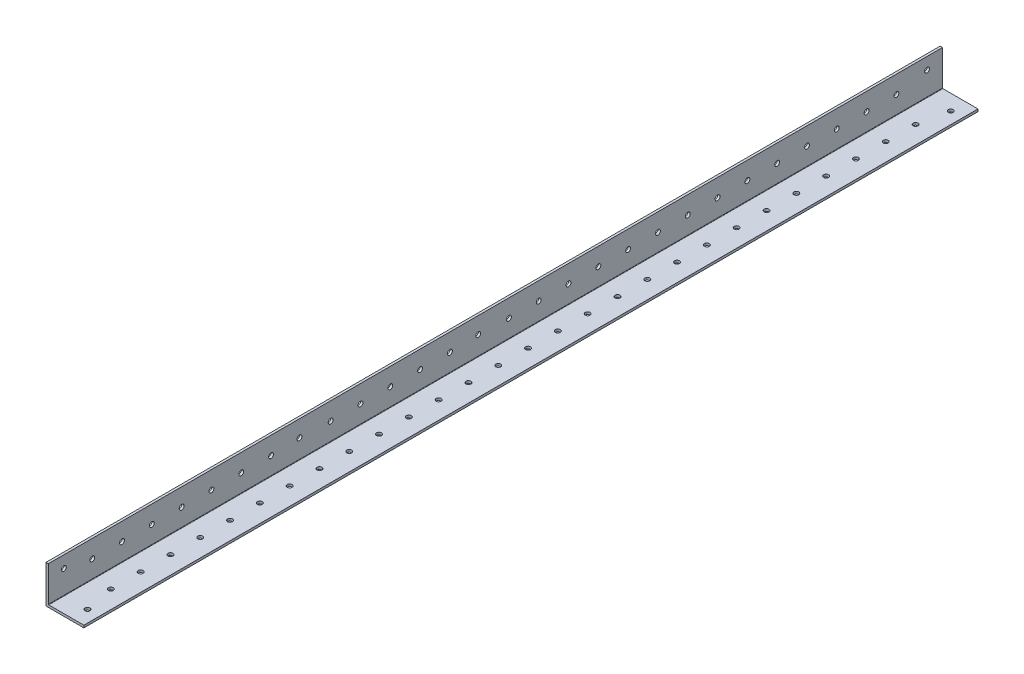
SolidWorks part; units mm, degrees
material "6061 Alloy"
ref_plane "Front Plane" through (0, 0, 0) normal (0, 0, 1) x (1, 0, 0)
ref_plane "Top Plane" through (0, 0, 0) normal (0, 1, 0) x (1, 0, 0)
ref_plane "Right Plane" through (0, 0, 0) normal (1, 0, 0) x (0, 0, -1)
sketch "Sketch1" plane through (0, 0, 0) normal (0, 0, 1) x (1, 0, 0)
  line L0 (0, 25.4) -> (0, 0) construction
  line L1 (0, 0) -> (25.4, 0) construction
  line L2 (25.4, 0) -> (25.4, 1.5875) construction
  line L3 (25.4, 1.5875) -> (1.5875, 1.5875) construction
  line L4 (1.5875, 1.5875) -> (1.5875, 25.4) construction
  line L6 (1.5875, 25.4) -> (0, 25.4) construction
  arc A0 (1.5875, 1.8415) -> (1.8415, 1.5875) centre (1.8415, 1.8415) ccw construction
  point P4 (0, 0)
  dimension "Inside Corner Radius" = 0.254
  dimension "Outside Height" = 25.4
  dimension "Inside Height" = 23.8125
  dimension "Outside Width" = 25.4
  dimension "Inside Width" = 23.8125
  dimension "Wall Thickness" = 1.5875
  dimension "Shape" = 90
sketch "Sketch2" plane through (0, 0, 0) normal (1, 0, 0) x (0, 0, -1)
  line L0 (1219.2, 0) -> (-1219.2, 0) construction
  line L1 (-1219.2, 25.4) -> (-1219.2, 0) construction
  line L2 (1219.2, 25.4) -> (1219.2, 0) construction
  point P0 (-1189.99, 0)
  point P4 (0, 0)
  point P6 (1189.99, 0)
  dimension "D1" = 29.21
  dimension "D2" = 29.21
  dimension "D3" = 25.4
  dimension "Length" = 2438.4
sketch "Sketch3" plane through (0, 0, 0) normal (0, 0, 1) x (1, 0, 0)
  line L0 (1.5875, 25.4) -> (0, 25.4)
  line L1 (0, 25.4) -> (0, 0)
  line L2 (0, 0) -> (25.4, 0)
  line L3 (25.4, 0) -> (25.4, 1.5875)
  line L4 (25.4, 1.5875) -> (1.5875, 1.5875)
  line L5 (1.5875, 1.5875) -> (1.5875, 25.4)
extrude "Boss-Extrude1" add sketch "Sketch3" along normal mid plane 2438.4
fillet "Fillet1" radius 0.254 1 edges at (1.5875, 1.5875, 0)
sketch "Sketch4" plane through (0, 0, 0) normal (-1, 0, 0) x (0, 0, 1)
  line L0 (1219.2, 25.4) -> (1219.2, 0) construction
  line L1 (-1219.2, 0) -> (619.2, 0)
  line L2 (-1219.2, 0) -> (-1219.2, 74.9453)
  line L3 (-1219.2, 74.9453) -> (619.2, 74.9453)
  line L4 (619.2, 0) -> (619.2, 74.9453)
  dimension "D1" = 600
extrude "Cut-Extrude1" cut sketch "Sketch4" against normal blind 60
sketch "Sketch5" plane through (0, 1.5875, 0) normal (0, 1, 0) x (1, 0, 0)
  line L0 (17.4625, -1208.8241) -> (17.4625, -1189.2) construction
  line L1 (13.4937, -649.2) -> (13.4937, -629.5759) construction
  line L3 (1.5875, -1189.2) -> (25.4, -1189.2) construction
  line L4 (1.5875, -1219.2) -> (1.5875, -619.2) construction
  line L5 (25.4, -1219.2) -> (25.4, -619.2) construction
  line L6 (13.4937, -629.5759) -> (17.4625, -629.5759) construction
  line L7 (17.4625, -629.5759) -> (13.4937, -629.5759) construction
  circle A30 centre (17.4625, -629.5759) radius 1.65
  circle A31 centre (17.4625, -1208.8241) radius 1.65
  circle A32 centre (13.4938, -1189.2) radius 1.65
  circle A33 centre (13.4938, -1169.2) radius 1.65
  circle A34 centre (13.4938, -1149.2) radius 1.65
  circle A35 centre (13.4938, -1129.2) radius 1.65
  circle A36 centre (13.4938, -1109.2) radius 1.65
  circle A37 centre (13.4938, -1089.2) radius 1.65
  circle A38 centre (13.4938, -1069.2) radius 1.65
  circle A39 centre (13.4938, -1049.2) radius 1.65
  circle A40 centre (13.4938, -1029.2) radius 1.65
  circle A41 centre (13.4938, -1009.2) radius 1.65
  circle A42 centre (13.4938, -989.2) radius 1.65
  circle A43 centre (13.4938, -969.2) radius 1.65
  circle A44 centre (13.4938, -949.2) radius 1.65
  circle A45 centre (13.4938, -929.2) radius 1.65
  circle A46 centre (13.4938, -909.2) radius 1.65
  circle A47 centre (13.4938, -889.2) radius 1.65
  circle A48 centre (13.4938, -869.2) radius 1.65
  circle A49 centre (13.4938, -849.2) radius 1.65
  circle A50 centre (13.4938, -829.2) radius 1.65
  circle A51 centre (13.4938, -809.2) radius 1.65
  circle A52 centre (13.4938, -789.2) radius 1.65
  circle A53 centre (13.4938, -769.2) radius 1.65
  circle A54 centre (13.4938, -749.2) radius 1.65
  circle A55 centre (13.4938, -729.2) radius 1.65
  circle A56 centre (13.4938, -709.2) radius 1.65
  circle A57 centre (13.4938, -689.2) radius 1.65
  circle A58 centre (13.4938, -669.2) radius 1.65
  circle A59 centre (13.4937, -649.2) radius 1.65
  dimension "D1" = 3.3
  dimension "D2" = 3.3
  dimension "D3" = 28
  dimension "D4" = 20
extrude "Cut-Extrude2" cut sketch "Sketch5" against normal blind 10
sketch "Sketch9" plane through (1.5875, 0, 0) normal (1, 0, 0) x (0, 0, -1)
  line L0 (-1205.7062, 212.5245) -> (-1205.7062, 4.3115) construction
  line L1 (-1206.4453, 212.5245) -> (-1204.9672, 212.5245) construction
  line L2 (-1203.8241, 4.3115) -> (-1213.8241, 4.3115) construction
  line L3 (-1207.4063, -6.3505) -> (-1204.0063, -6.3505) construction
  line L4 (-634.3937, -3.175) -> (-630.9937, -3.175) construction
  line L5 (-634.3937, 0) -> (-634.3937, -6.35) construction
  line L6 (-630.9937, -6.35) -> (-630.9937, 0) construction
  line L7 (-1219.2, 1.5875) -> (-619.2, 1.5875) construction
  line L8 (-1189.7652, 25.4) -> (-1189.7652, 1.5875) construction
  line L9 (-1219.2, 25.4) -> (-619.2, 25.4) construction
  line L10 (-650.1411, 189.6802) -> (-650.1411, 177.774) construction
  line L11 (-1189.7652, 189.6802) -> (-1189.7652, 177.774) construction
  line L12 (-1219.2, 177.774) -> (-619.2, 177.774) construction
  line L16 (-629.5759, 17.4625) -> (-629.5759, 3.8186) construction
  line L17 (-623.0735, 3.8186) -> (-633.4875, 3.8186) construction
  line L18 (-650.1411, 13.4937) -> (-629.5759, 13.4937) construction
  circle A0 centre (-629.5759, 17.4625) radius 1.65
  circle A3 centre (-1208.8241, 17.4625) radius 1.65
  circle A16 centre (-1050.7062, 14.2875) radius 1.65
  circle A32 centre (-930.7062, 14.2875) radius 1.65
  circle A33 centre (-1189.7652, 13.4937) radius 1.65
  circle A34 centre (-1169.7652, 13.4937) radius 1.65
  circle A35 centre (-1149.7652, 13.4937) radius 1.65
  circle A36 centre (-1129.7652, 13.4937) radius 1.65
  circle A37 centre (-1109.7652, 13.4937) radius 1.65
  circle A38 centre (-1089.7652, 13.4937) radius 1.65
  circle A39 centre (-1069.7652, 13.4937) radius 1.65
  circle A40 centre (-1029.7652, 13.4937) radius 1.65
  circle A41 centre (-1009.7652, 13.4937) radius 1.65
  circle A42 centre (-989.7652, 13.4937) radius 1.65
  circle A43 centre (-969.7652, 13.4937) radius 1.65
  circle A44 centre (-949.7652, 13.4937) radius 1.65
  circle A73 centre (-650.1411, 13.4937) radius 1.65
  circle A75 centre (-670.1411, 13.4937) radius 1.65
  circle A76 centre (-690.1411, 13.4937) radius 1.65
  circle A77 centre (-710.1411, 13.4937) radius 1.65
  circle A78 centre (-730.1411, 13.4937) radius 1.65
  circle A79 centre (-750.1411, 13.4937) radius 1.65
  circle A80 centre (-770.1411, 13.4937) radius 1.65
  circle A81 centre (-790.1411, 13.4937) radius 1.65
  circle A94 centre (-810.1411, 13.4937) radius 1.65
  circle A95 centre (-830.1411, 13.4937) radius 1.65
  circle A96 centre (-850.1411, 13.4937) radius 1.65
  circle A97 centre (-870.1411, 13.4937) radius 1.65
  circle A98 centre (-890.1411, 13.4937) radius 1.65
  circle A99 centre (-910.1411, 13.4937) radius 1.65
  dimension "D1" = 3.3
  dimension "D3" = 3.3
  dimension "D4" = 275
  dimension "D7" = 7
  dimension "D2" = 155
  dimension "D5" = 12.7
  dimension "D6" = 3.3
  dimension "D10" = 14
  dimension "D11" = 20
  dimension "D12" = 20
  dimension "D13" = 20
  dimension "D14" = 3.3
  dimension "D8" = 40
  dimension "D9" = 5
extrude "Cut-Extrude6" cut sketch "Sketch9" against normal blind 60
equation "\"D1@Boss-Extrude1\"=\"Length@Sketch2\""
equation "\"D1@Sketch2\" = \"Outside Width@Sketch1\" * 1.15"
equation "\"D2@Sketch2\"=\"D1@Sketch2\""
equation "\"D1@Fillet1\"=\"Inside Corner Radius@Sketch1\""
equation "\"D3@Sketch2\"=\"Outside Height@Sketch1\""
